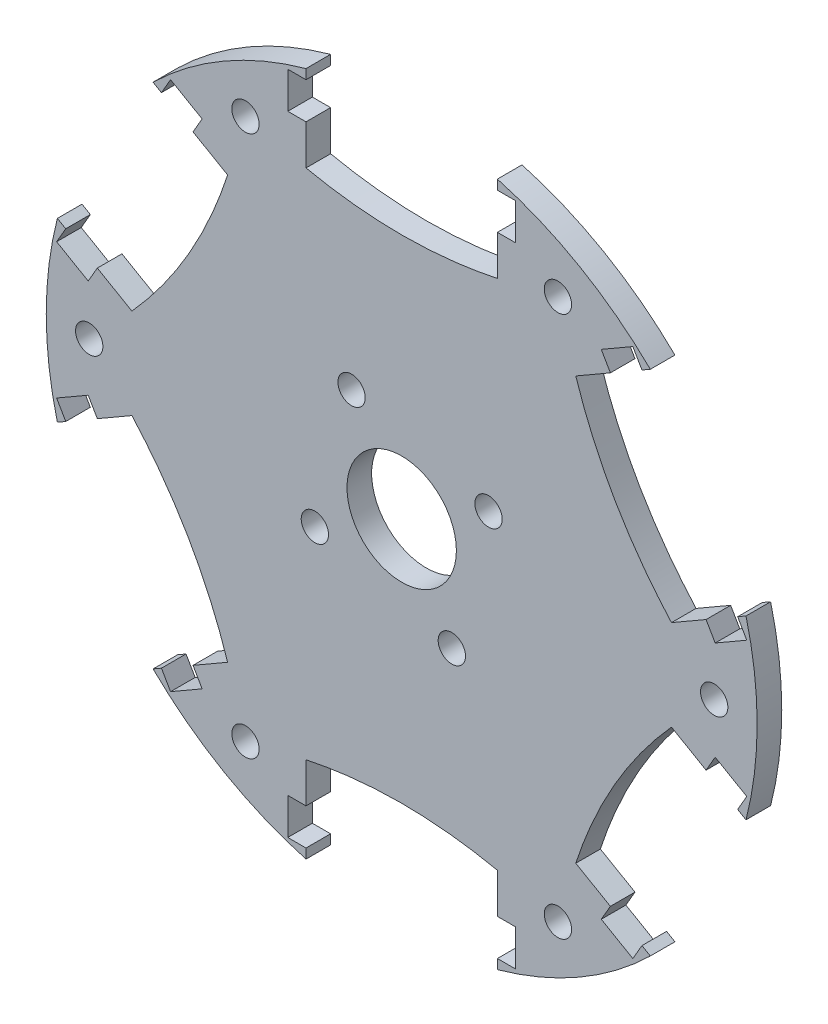
SolidWorks part; units mm, degrees
ref_plane "Alzado" through (0, 0, 0) normal (0, 0, 1) x (1, 0, 0)
ref_plane "Planta" through (0, 0, 0) normal (0, 1, 0) x (1, 0, 0)
ref_plane "Vista lateral" through (0, 0, 0) normal (1, 0, 0) x (0, 0, -1)
sketch "Croquis2" plane through (0, 0, 0) normal (0, 0, 1) x (1, 0, 0)
  line L0 (0, 0) -> (0, 41) construction
  line L1 (-9.5, 34.5) -> (9.5, 34.5) construction
  line L2 (0, 0) -> (41, 0) construction
  line L3 (-9.5, 29.1158) -> (-9.5, 39.8842) construction
  line L4 (9.5, 29.1158) -> (9.5, 39.8842) construction
  line L5 (-10.5, 37.56) -> (-10.5, 28.1158)
  line L6 (10.5, 37.56) -> (10.5, 28.1158)
  line L7 (27.2779, 27.8732) -> (19.099, 23.1512)
  line L8 (37.7779, 9.6867) -> (29.599, 4.9646)
  line L9 (37.7779, -9.6867) -> (29.599, -4.9646)
  line L10 (27.2779, -27.8732) -> (19.099, -23.1512)
  line L11 (10.5, -37.56) -> (10.5, -28.1158)
  line L12 (-10.5, -37.56) -> (-10.5, -28.1158)
  line L13 (-27.2779, -27.8732) -> (-19.099, -23.1512)
  line L14 (-37.7779, -9.6867) -> (-29.599, -4.9646)
  line L15 (-37.7779, 9.6867) -> (-29.599, 4.9646)
  line L16 (-27.2779, 27.8732) -> (-19.099, 23.1512)
  line L17 (10.5, 28.1158) -> (19.099, 23.1512) construction
  line L18 (0, 0) -> (17.892, 30.9899) construction
  circle A0 centre (0, 0) radius 41 construction
  circle A1 centre (0, 0) radius 39
  circle A2 centre (0, 0) radius 6
  circle A3 centre (0, 0) radius 35.7841 construction
  circle A5 centre (17.142, 29.6909) radius 1.5
  circle A6 centre (34.2841, 0) radius 1.5
  circle A7 centre (17.142, -29.6909) radius 1.5
  circle A8 centre (-17.142, -29.6909) radius 1.5
  circle A9 centre (-34.2841, 0) radius 1.5
  circle A10 centre (-17.142, 29.6909) radius 1.5
  spline S0 degree 2 poles (-9.5, 29.1158) (0, 26.8842) (9.5, 29.1158) knots 0 0 0 1 1 1 construction
  spline S1 degree 2 poles (-10.5, 28.1158) (0, 25.8842) (10.5, 28.1158) knots 0 0 0 1 1 1
  spline S2 degree 2 poles (19.099, 23.1512) (22.4164, 12.9421) (29.599, 4.9646) knots 0 0 0 1 1 1
  spline S3 degree 2 poles (29.599, -4.9646) (22.4164, -12.9421) (19.099, -23.1512) knots 0 0 0 1 1 1
  spline S4 degree 2 poles (10.5, -28.1158) (0, -25.8842) (-10.5, -28.1158) knots 0 0 0 1 1 1
  spline S5 degree 2 poles (-19.099, -23.1512) (-22.4164, -12.9421) (-29.599, -4.9646) knots 0 0 0 1 1 1
  spline S6 degree 2 poles (-29.599, 4.9646) (-22.4164, 12.9421) (-19.099, 23.1512) knots 0 0 0 1 1 1
  point P6 (0, 34.5)
  point P46 (14.7995, 25.6335)
  dimension "D1" = 82
  dimension "D4" = 78
  dimension "D10" = 12
  dimension "D11" = 3
  dimension "D12" = 6
  dimension "D2" = 34.5
  dimension "D3" = 19
  dimension "D5" = 6.5
  dimension "D6" = 1
  dimension "D7" = 1
  dimension "D8" = 1
  dimension "D9" = 6
extrude "Saliente-Extruir2" add sketch "Croquis2" along normal blind 2.7 contours S6 L15 A1 L14 S5 L13 L12 S4 L11 L10 S3 L9 L8 S2 L7 L6 S1 L5 L16 A10 A9 A8 A7 A6 A5 A2
sketch "Croquis3" plane through (0, 0, 2.7) normal (0, 0, 1) x (1, 0, 0)
  line L0 (0, 0) -> (0, 41) construction
  line L1 (-12.5, 34.5) -> (12.5, 34.5) construction
  line L2 (0, 0) -> (41, 0) construction
  line L3 (-10.5, 36.5) -> (-12.5, 36.5)
  line L4 (-10.5, 37.56) -> (-10.5, 28.1158) construction
  line L5 (-12.5, 36.5) -> (-12.5, 32.5)
  line L6 (-10.5, 32.5) -> (-12.5, 32.5)
  line L7 (-10.5, 36.5) -> (-10.5, 32.5)
  line L8 (10.5, 36.5) -> (12.5, 36.5)
  line L9 (12.5, 36.5) -> (12.5, 32.5)
  line L10 (10.5, 32.5) -> (12.5, 32.5)
  line L11 (10.5, 36.5) -> (10.5, 32.5)
  line L12 (22.8958, 25.3433) -> (21.8958, 27.0753)
  line L13 (26.3599, 27.3433) -> (22.8958, 25.3433)
  line L14 (25.3599, 29.0753) -> (21.8958, 27.0753)
  line L15 (26.3599, 27.3433) -> (25.3599, 29.0753)
  line L16 (36.8599, 9.1567) -> (37.8599, 7.4247)
  line L17 (37.8599, 7.4247) -> (34.3958, 5.4247)
  line L18 (33.3958, 7.1567) -> (34.3958, 5.4247)
  line L19 (36.8599, 9.1567) -> (33.3958, 7.1567)
  line L20 (33.3958, -7.1567) -> (34.3958, -5.4247)
  line L21 (36.8599, -9.1567) -> (33.3958, -7.1567)
  line L22 (37.8599, -7.4247) -> (34.3958, -5.4247)
  line L23 (36.8599, -9.1567) -> (37.8599, -7.4247)
  line L24 (26.3599, -27.3433) -> (25.3599, -29.0753)
  line L25 (25.3599, -29.0753) -> (21.8958, -27.0753)
  line L26 (22.8958, -25.3433) -> (21.8958, -27.0753)
  line L27 (26.3599, -27.3433) -> (22.8958, -25.3433)
  line L28 (10.5, -32.5) -> (12.5, -32.5)
  line L29 (10.5, -36.5) -> (10.5, -32.5)
  line L30 (12.5, -36.5) -> (12.5, -32.5)
  line L31 (10.5, -36.5) -> (12.5, -36.5)
  line L32 (-10.5, -36.5) -> (-12.5, -36.5)
  line L33 (-12.5, -36.5) -> (-12.5, -32.5)
  line L34 (-10.5, -32.5) -> (-12.5, -32.5)
  line L35 (-10.5, -36.5) -> (-10.5, -32.5)
  line L36 (-22.8958, -25.3433) -> (-21.8958, -27.0753)
  line L37 (-26.3599, -27.3433) -> (-22.8958, -25.3433)
  line L38 (-25.3599, -29.0753) -> (-21.8958, -27.0753)
  line L39 (-26.3599, -27.3433) -> (-25.3599, -29.0753)
  line L40 (-36.8599, -9.1567) -> (-37.8599, -7.4247)
  line L41 (-37.8599, -7.4247) -> (-34.3958, -5.4247)
  line L42 (-33.3958, -7.1567) -> (-34.3958, -5.4247)
  line L43 (-36.8599, -9.1567) -> (-33.3958, -7.1567)
  line L44 (-33.3958, 7.1567) -> (-34.3958, 5.4247)
  line L45 (-36.8599, 9.1567) -> (-33.3958, 7.1567)
  line L46 (-37.8599, 7.4247) -> (-34.3958, 5.4247)
  line L47 (-36.8599, 9.1567) -> (-37.8599, 7.4247)
  line L48 (-26.3599, 27.3433) -> (-25.3599, 29.0753)
  line L49 (-25.3599, 29.0753) -> (-21.8958, 27.0753)
  line L50 (-22.8958, 25.3433) -> (-21.8958, 27.0753)
  line L51 (-26.3599, 27.3433) -> (-22.8958, 25.3433)
  line L52 (24.6279, 26.3433) -> (35.1279, 8.1567) construction
  line L53 (29.8779, 17.25) -> (0, 0) construction
  circle A0 centre (0, 0) radius 11 construction
  circle A1 centre (11, 0) radius 1.5 construction
  circle A2 centre (0, -11) radius 1.5 construction
  circle A3 centre (-11, 0) radius 1.5 construction
  circle A4 centre (0, 11) radius 1.5 construction
  circle A5 centre (0, 0) radius 41 construction
  circle A6 centre (9.5263, 5.5) radius 1.5
  circle A7 centre (5.5, -9.5263) radius 1.5
  circle A8 centre (-9.5263, -5.5) radius 1.5
  circle A9 centre (-5.5, 9.5263) radius 1.5
  point P15 (0, 34.5)
  dimension "D1" = 22
  dimension "D2" = 3
  dimension "D4" = 82
  dimension "D9" = 3
  dimension "D5" = 34.5
  dimension "D6" = 25
  dimension "D7" = 2
  dimension "D8" = 6
  dimension "D3" = 4
  dimension "D10" = 4
extrude "Cortar-Extruir1" cut sketch "Croquis3" against normal through all and the other way through all
